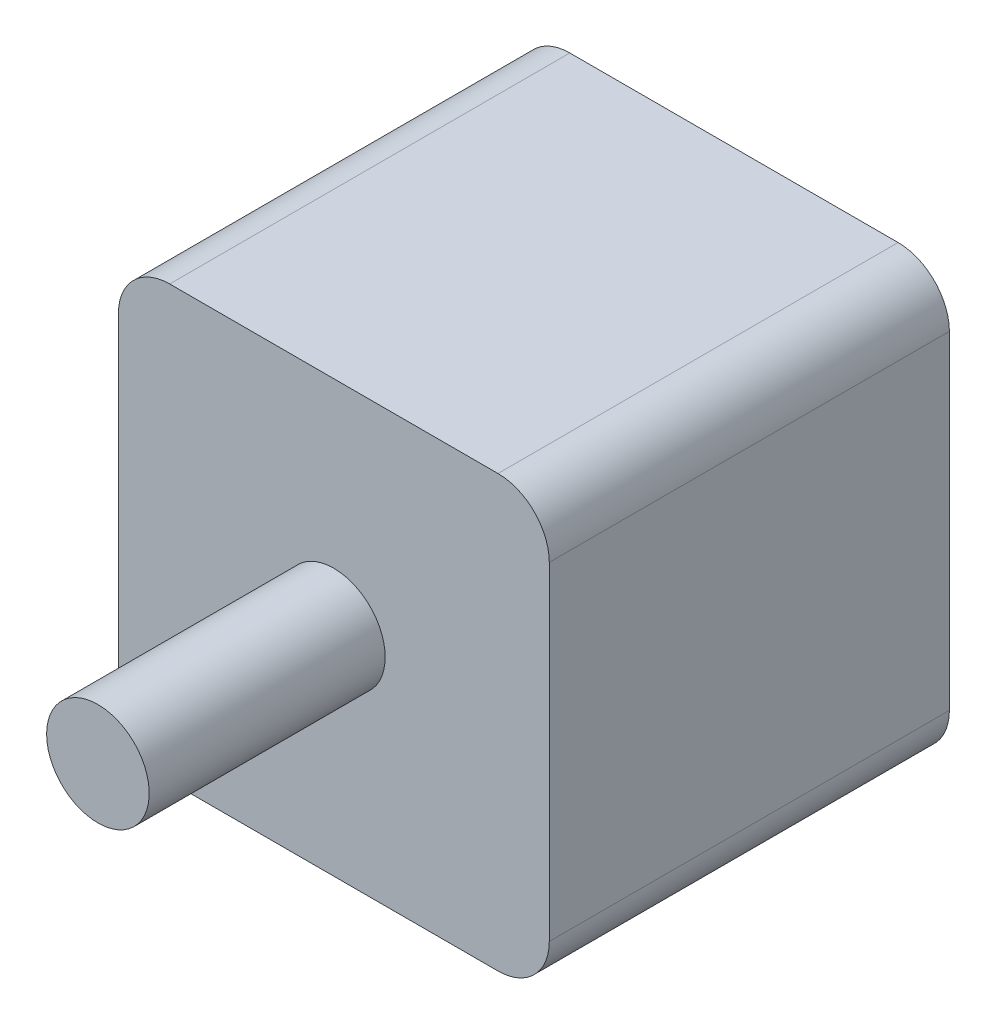
SolidWorks part; units mm, degrees
ref_plane "Plan de face" through (0, 0, 0) normal (0, 0, 1) x (1, 0, 0)
ref_plane "Plan de dessus" through (0, 0, 0) normal (0, 1, 0) x (1, 0, 0)
ref_plane "Plan de droite" through (0, 0, 0) normal (1, 0, 0) x (0, 0, -1)
sketch "Esquisse1" plane through (0, 0, 0) normal (0, 0, 1) x (1, 0, 0)
  line L1 (0, 0) -> (42, 0)
  line L2 (0, 0) -> (0, -42)
  line L3 (0, -42) -> (42, -42)
  line L4 (42, 0) -> (42, -42)
  dimension "D1" = 42
  dimension "D2" = 42
extrude "Boss.-Extru.1" add sketch "Esquisse1" along normal blind 39
fillet "Congé1" radius 5 4 edges at (42, -42, 19.5) (0, -42, 19.5) (0, 0, 19.5) (42, 0, 19.5)
sketch "Esquisse2" plane through (0, 0, 0) normal (0, 0, -1) x (-1, 0, 0)
  line L0 (0, 0) -> (0, -44.9052) construction
  line L1 (0, -44.9052) -> (-40.5355, -1.4645) construction
  line L2 (-40.5355, -1.4645) -> (-1.4645, -1.4645) construction
  line L3 (-1.4645, -1.4645) -> (-1.4645, -40.5355) construction
  line L4 (-1.4645, -40.5355) -> (-40.5355, -40.5355) construction
  line L5 (-40.5355, -40.5355) -> (-1.4645, -1.4645) construction
  line L6 (-1.4645, -1.4645) -> (-21, -21) construction
  line L7 (-21, -21) -> (-1.4645, -40.5355) construction
  arc A0 (-37, 0) -> (-42, -5) centre (-37, -5) ccw construction
  arc A1 (0, -5) -> (-5, 0) centre (-5, -5) ccw construction
  arc A2 (-5, -42) -> (0, -37) centre (-5, -37) ccw construction
  arc A3 (-42, -37) -> (-37, -42) centre (-37, -37) ccw construction
  circle A4 centre (-21, -21) radius 5
extrude "Boss.-Extru.2" add sketch "Esquisse2" along normal blind 23
sketch "Esquisse3" plane through (0, 0, -23) normal (0, 0, -1) x (-1, 0, 0)
  circle A0 centre (-21, -21) radius 5
extrude "Boss.-Extru.3" add sketch "Esquisse3" against normal blind 85
sketch "Esquisse4" plane through (0, 0, -23) normal (0, 0, -1) x (-1, 0, 0)
  circle A0 centre (-21, -21) radius 5
extrude "Enlèv. mat.-Extru.1" cut sketch "Esquisse4" against normal blind 23
